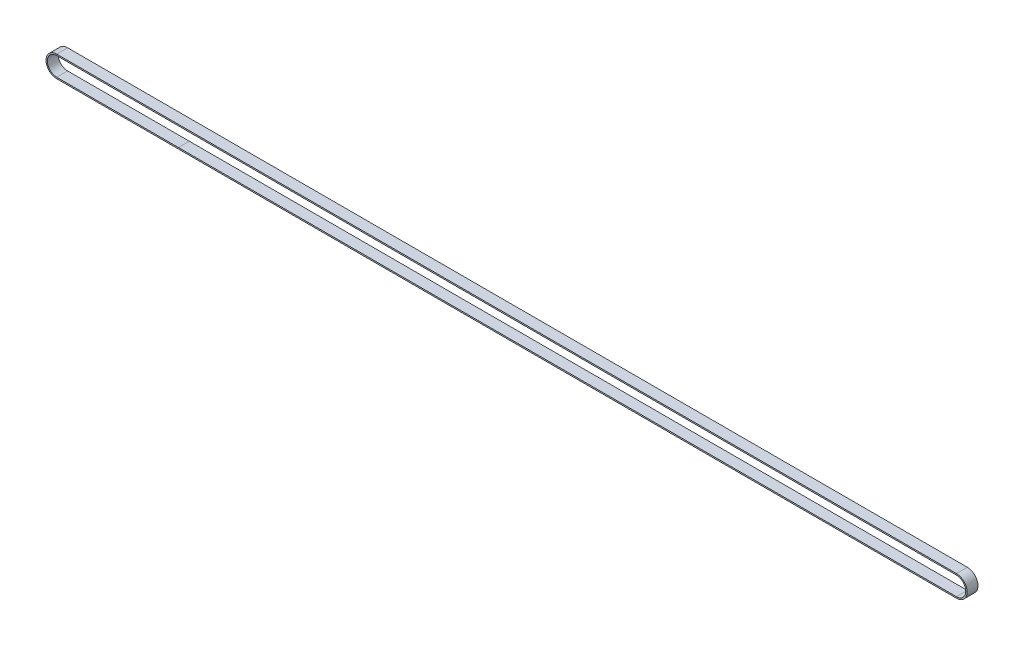
SolidWorks part; units mm, degrees
ref_plane "Front Plane" through (0, 0, 0) normal (0, 0, 1) x (1, 0, 0)
ref_plane "Top Plane" through (0, 0, 0) normal (0, 1, 0) x (1, 0, 0)
ref_plane "Right Plane" through (0, 0, 0) normal (1, 0, 0) x (0, 0, -1)
sketch "Sketch1" plane through (0, 0, 0) normal (0, 0, 1) x (1, 0, 0)
  line L0 (-149.0919, 9.0907) -> (346.9081, 9.0907)
  line L1 (-148.8622, -1.9593) -> (-148.9877, -1.9593)
  line L2 (-148.8622, -1.9593) -> (-148.8621, -1.9593)
  line L3 (-146.8622, -1.9593) -> (-146.8621, -1.9593)
  line L4 (-147.1989, -1.9593) -> (-146.8622, -1.9593)
  line L5 (-145.1989, -1.9593) -> (-144.8622, -1.9593)
  line L6 (-144.8622, -1.9593) -> (-144.8621, -1.9593)
  line L7 (-143.1989, -1.9593) -> (-142.8622, -1.9593)
  line L8 (-142.8622, -1.9593) -> (-142.8621, -1.9593)
  line L9 (-141.1989, -1.9593) -> (-140.8622, -1.9593)
  line L10 (-140.8622, -1.9593) -> (-140.8621, -1.9593)
  line L11 (-139.1989, -1.9593) -> (-138.8622, -1.9593)
  line L12 (-138.8622, -1.9593) -> (-138.8621, -1.9593)
  line L13 (-137.1989, -1.9593) -> (-136.8622, -1.9593)
  line L14 (-136.8622, -1.9593) -> (-136.8621, -1.9593)
  line L15 (-135.1989, -1.9593) -> (-134.8622, -1.9593)
  line L16 (-134.8622, -1.9593) -> (-134.8621, -1.9593)
  line L17 (-133.1989, -1.9593) -> (-132.8622, -1.9593)
  line L18 (-132.8622, -1.9593) -> (-132.8621, -1.9593)
  line L19 (-131.1989, -1.9593) -> (-130.8622, -1.9593)
  line L20 (-130.8622, -1.9593) -> (-130.8621, -1.9593)
  line L21 (-129.1989, -1.9593) -> (-128.8622, -1.9593)
  line L22 (-128.8622, -1.9593) -> (-128.8621, -1.9593)
  line L23 (-127.1989, -1.9593) -> (-126.8622, -1.9593)
  line L24 (-126.8622, -1.9593) -> (-126.8621, -1.9593)
  line L25 (-125.1989, -1.9593) -> (-124.8622, -1.9593)
  line L26 (-124.8622, -1.9593) -> (-124.8621, -1.9593)
  line L27 (-123.1989, -1.9593) -> (-122.8622, -1.9593)
  line L28 (-122.8622, -1.9593) -> (-122.8621, -1.9593)
  line L29 (-121.1989, -1.9593) -> (-120.8622, -1.9593)
  line L30 (-120.8622, -1.9593) -> (-120.8621, -1.9593)
  line L31 (-119.1989, -1.9593) -> (-118.8622, -1.9593)
  line L32 (-118.8622, -1.9593) -> (-118.8621, -1.9593)
  line L33 (-117.1989, -1.9593) -> (-116.8622, -1.9593)
  line L34 (-116.8622, -1.9593) -> (-116.8621, -1.9593)
  line L35 (-115.1989, -1.9593) -> (-114.8622, -1.9593)
  line L36 (-114.8622, -1.9593) -> (-114.8621, -1.9593)
  line L37 (-113.1989, -1.9593) -> (-112.8622, -1.9593)
  line L38 (-112.8622, -1.9593) -> (-112.8621, -1.9593)
  line L39 (-111.1989, -1.9593) -> (-110.8622, -1.9593)
  line L40 (-110.8622, -1.9593) -> (-110.8621, -1.9593)
  line L41 (-109.1989, -1.9593) -> (-108.8622, -1.9593)
  line L42 (-108.8622, -1.9593) -> (-108.8621, -1.9593)
  line L43 (-107.1989, -1.9593) -> (-106.8622, -1.9593)
  line L44 (-106.8622, -1.9593) -> (-106.8621, -1.9593)
  line L45 (-105.1989, -1.9593) -> (-104.8622, -1.9593)
  line L46 (-104.8622, -1.9593) -> (-104.8621, -1.9593)
  line L47 (-103.1989, -1.9593) -> (-102.8622, -1.9593)
  line L48 (-102.8622, -1.9593) -> (-102.8621, -1.9593)
  line L49 (-101.1989, -1.9593) -> (-100.8622, -1.9593)
  line L50 (-100.8622, -1.9593) -> (-100.8621, -1.9593)
  line L51 (-99.1989, -1.9593) -> (-98.8622, -1.9593)
  line L52 (-98.8622, -1.9593) -> (-98.8621, -1.9593)
  line L53 (-97.1989, -1.9593) -> (-96.8622, -1.9593)
  line L54 (-96.8622, -1.9593) -> (-96.8621, -1.9593)
  line L55 (-95.1989, -1.9593) -> (-94.8622, -1.9593)
  line L56 (-94.8622, -1.9593) -> (-94.8621, -1.9593)
  line L57 (-93.1989, -1.9593) -> (-92.8622, -1.9593)
  line L58 (-92.8622, -1.9593) -> (-92.8621, -1.9593)
  line L59 (-91.1989, -1.9593) -> (-90.8622, -1.9593)
  line L60 (-90.8622, -1.9593) -> (-90.8621, -1.9593)
  line L61 (-89.1989, -1.9593) -> (-88.8622, -1.9593)
  line L62 (-88.8622, -1.9593) -> (-88.8621, -1.9593)
  line L63 (-87.1989, -1.9593) -> (-86.8622, -1.9593)
  line L64 (-86.8622, -1.9593) -> (-86.8621, -1.9593)
  line L65 (-85.1989, -1.9593) -> (-84.8622, -1.9593)
  line L66 (-84.8622, -1.9593) -> (-84.8621, -1.9593)
  line L277 (346.9081, 3.1907) -> (-46.1296, 3.1907) construction
  line L278 (-83.1989, 8.3407) -> (346.9081, 8.3407)
  line L279 (-149.0919, -2.7093) -> (346.9081, -2.7093)
  line L280 (-149.1969, 8.3407) -> (-148.8622, 8.3407)
  line L491 (-84.8622, 8.3407) -> (-84.8621, 8.3407)
  line L492 (-85.1989, 8.3407) -> (-84.8622, 8.3407)
  line L493 (-86.8622, 8.3407) -> (-86.8621, 8.3407)
  line L494 (-87.1989, 8.3407) -> (-86.8622, 8.3407)
  line L495 (-88.8622, 8.3407) -> (-88.8621, 8.3407)
  line L496 (-89.1989, 8.3407) -> (-88.8622, 8.3407)
  line L497 (-90.8622, 8.3407) -> (-90.8621, 8.3407)
  line L498 (-91.1989, 8.3407) -> (-90.8622, 8.3407)
  line L499 (-92.8622, 8.3407) -> (-92.8621, 8.3407)
  line L500 (-93.1989, 8.3407) -> (-92.8622, 8.3407)
  line L501 (-94.8622, 8.3407) -> (-94.8621, 8.3407)
  line L502 (-95.1989, 8.3407) -> (-94.8622, 8.3407)
  line L503 (-96.8622, 8.3407) -> (-96.8621, 8.3407)
  line L504 (-97.1989, 8.3407) -> (-96.8622, 8.3407)
  line L505 (-98.8622, 8.3407) -> (-98.8621, 8.3407)
  line L506 (-99.1989, 8.3407) -> (-98.8622, 8.3407)
  line L507 (-100.8622, 8.3407) -> (-100.8621, 8.3407)
  line L508 (-101.1989, 8.3407) -> (-100.8622, 8.3407)
  line L509 (-102.8622, 8.3407) -> (-102.8621, 8.3407)
  line L510 (-103.1989, 8.3407) -> (-102.8622, 8.3407)
  line L511 (-104.8622, 8.3407) -> (-104.8621, 8.3407)
  line L512 (-105.1989, 8.3407) -> (-104.8622, 8.3407)
  line L513 (-106.8622, 8.3407) -> (-106.8621, 8.3407)
  line L514 (-107.1989, 8.3407) -> (-106.8622, 8.3407)
  line L515 (-108.8622, 8.3407) -> (-108.8621, 8.3407)
  line L516 (-109.1989, 8.3407) -> (-108.8622, 8.3407)
  line L517 (-110.8622, 8.3407) -> (-110.8621, 8.3407)
  line L518 (-111.1989, 8.3407) -> (-110.8622, 8.3407)
  line L519 (-112.8622, 8.3407) -> (-112.8621, 8.3407)
  line L520 (-113.1989, 8.3407) -> (-112.8622, 8.3407)
  line L521 (-114.8622, 8.3407) -> (-114.8621, 8.3407)
  line L522 (-115.1989, 8.3407) -> (-114.8622, 8.3407)
  line L523 (-116.8622, 8.3407) -> (-116.8621, 8.3407)
  line L524 (-117.1989, 8.3407) -> (-116.8622, 8.3407)
  line L525 (-118.8622, 8.3407) -> (-118.8621, 8.3407)
  line L526 (-119.1989, 8.3407) -> (-118.8622, 8.3407)
  line L527 (-120.8622, 8.3407) -> (-120.8621, 8.3407)
  line L528 (-121.1989, 8.3407) -> (-120.8622, 8.3407)
  line L529 (-122.8622, 8.3407) -> (-122.8621, 8.3407)
  line L530 (-123.1989, 8.3407) -> (-122.8622, 8.3407)
  line L531 (-124.8622, 8.3407) -> (-124.8621, 8.3407)
  line L532 (-125.1989, 8.3407) -> (-124.8622, 8.3407)
  line L533 (-126.8622, 8.3407) -> (-126.8621, 8.3407)
  line L534 (-127.1989, 8.3407) -> (-126.8622, 8.3407)
  line L535 (-128.8622, 8.3407) -> (-128.8621, 8.3407)
  line L536 (-129.1989, 8.3407) -> (-128.8622, 8.3407)
  line L537 (-130.8622, 8.3407) -> (-130.8621, 8.3407)
  line L538 (-131.1989, 8.3407) -> (-130.8622, 8.3407)
  line L539 (-132.8622, 8.3407) -> (-132.8621, 8.3407)
  line L540 (-133.1989, 8.3407) -> (-132.8622, 8.3407)
  line L541 (-134.8622, 8.3407) -> (-134.8621, 8.3407)
  line L542 (-135.1989, 8.3407) -> (-134.8622, 8.3407)
  line L543 (-136.8622, 8.3407) -> (-136.8621, 8.3407)
  line L544 (-137.1989, 8.3407) -> (-136.8622, 8.3407)
  line L545 (-138.8622, 8.3407) -> (-138.8621, 8.3407)
  line L546 (-139.1989, 8.3407) -> (-138.8622, 8.3407)
  line L547 (-140.8622, 8.3407) -> (-140.8621, 8.3407)
  line L548 (-141.1989, 8.3407) -> (-140.8622, 8.3407)
  line L549 (-142.8622, 8.3407) -> (-142.8621, 8.3407)
  line L550 (-143.1989, 8.3407) -> (-142.8622, 8.3407)
  line L551 (-144.8622, 8.3407) -> (-144.8621, 8.3407)
  line L552 (-145.1989, 8.3407) -> (-144.8622, 8.3407)
  line L553 (-147.1989, 8.3407) -> (-146.8622, 8.3407)
  line L554 (-146.8622, 8.3407) -> (-146.8621, 8.3407)
  line L555 (-148.8622, 8.3407) -> (-148.8621, 8.3407)
  line L556 (-83.1989, -1.9593) -> (346.9081, -1.9593)
  arc A0 (-149.1969, 8.3407) -> (-148.9869, -1.9593) centre (-149.0919, 3.1907) ccw
  arc A1 (346.9081, -1.9593) -> (346.9081, 8.3407) centre (346.9081, 3.1907) ccw
  arc A2 (-146.8621, -1.9593) -> (-146.7228, -1.8564) centre (-146.9197, -1.7354) ccw
  arc A3 (-148.8621, -1.9593) -> (-148.7228, -1.8564) centre (-148.9197, -1.7354) ccw
  arc A4 (-148.7228, -1.8564) -> (-148.6336, -1.611) centre (-149.2769, -1.5162) ccw
  arc A5 (-147.4274, -1.611) -> (-148.6336, -1.611) centre (-148.0305, -1.6999) ccw
  arc A6 (-147.4274, -1.611) -> (-147.3383, -1.8564) centre (-146.7842, -1.5162) ccw
  arc A7 (-147.3383, -1.8564) -> (-147.1989, -1.9593) centre (-147.1413, -1.7354) ccw
  arc A8 (-146.7228, -1.8564) -> (-146.6336, -1.611) centre (-147.2769, -1.5162) ccw
  arc A9 (-145.4274, -1.611) -> (-146.6336, -1.611) centre (-146.0305, -1.6999) ccw
  arc A10 (-145.4274, -1.611) -> (-145.3383, -1.8564) centre (-144.7842, -1.5162) ccw
  arc A11 (-145.3383, -1.8564) -> (-145.1989, -1.9593) centre (-145.1413, -1.7354) ccw
  arc A12 (-144.8621, -1.9593) -> (-144.7228, -1.8564) centre (-144.9197, -1.7354) ccw
  arc A13 (-144.7228, -1.8564) -> (-144.6336, -1.611) centre (-145.2769, -1.5162) ccw
  arc A14 (-143.4274, -1.611) -> (-144.6336, -1.611) centre (-144.0305, -1.6999) ccw
  arc A15 (-143.4274, -1.611) -> (-143.3383, -1.8564) centre (-142.7842, -1.5162) ccw
  arc A16 (-143.3383, -1.8564) -> (-143.1989, -1.9593) centre (-143.1413, -1.7354) ccw
  arc A17 (-142.8621, -1.9593) -> (-142.7228, -1.8564) centre (-142.9197, -1.7354) ccw
  arc A18 (-142.7228, -1.8564) -> (-142.6336, -1.611) centre (-143.2769, -1.5162) ccw
  arc A19 (-141.4274, -1.611) -> (-142.6336, -1.611) centre (-142.0305, -1.6999) ccw
  arc A20 (-141.4274, -1.611) -> (-141.3383, -1.8564) centre (-140.7842, -1.5162) ccw
  arc A21 (-141.3383, -1.8564) -> (-141.1989, -1.9593) centre (-141.1413, -1.7354) ccw
  arc A22 (-140.8621, -1.9593) -> (-140.7228, -1.8564) centre (-140.9197, -1.7354) ccw
  arc A23 (-140.7228, -1.8564) -> (-140.6336, -1.611) centre (-141.2769, -1.5162) ccw
  arc A24 (-139.4274, -1.611) -> (-140.6336, -1.611) centre (-140.0305, -1.6999) ccw
  arc A25 (-139.4274, -1.611) -> (-139.3383, -1.8564) centre (-138.7842, -1.5162) ccw
  arc A26 (-139.3383, -1.8564) -> (-139.1989, -1.9593) centre (-139.1413, -1.7354) ccw
  arc A27 (-138.8621, -1.9593) -> (-138.7228, -1.8564) centre (-138.9197, -1.7354) ccw
  arc A28 (-138.7228, -1.8564) -> (-138.6336, -1.611) centre (-139.2769, -1.5162) ccw
  arc A29 (-137.4274, -1.611) -> (-138.6336, -1.611) centre (-138.0305, -1.6999) ccw
  arc A30 (-137.4274, -1.611) -> (-137.3383, -1.8564) centre (-136.7842, -1.5162) ccw
  arc A31 (-137.3383, -1.8564) -> (-137.1989, -1.9593) centre (-137.1413, -1.7354) ccw
  arc A32 (-136.8621, -1.9593) -> (-136.7228, -1.8564) centre (-136.9197, -1.7354) ccw
  arc A33 (-136.7228, -1.8564) -> (-136.6336, -1.611) centre (-137.2769, -1.5162) ccw
  arc A34 (-135.4274, -1.611) -> (-136.6336, -1.611) centre (-136.0305, -1.6999) ccw
  arc A35 (-135.4274, -1.611) -> (-135.3383, -1.8564) centre (-134.7842, -1.5162) ccw
  arc A36 (-135.3383, -1.8564) -> (-135.1989, -1.9593) centre (-135.1413, -1.7354) ccw
  arc A37 (-134.8621, -1.9593) -> (-134.7228, -1.8564) centre (-134.9197, -1.7354) ccw
  arc A38 (-134.7228, -1.8564) -> (-134.6336, -1.611) centre (-135.2769, -1.5162) ccw
  arc A39 (-133.4274, -1.611) -> (-134.6336, -1.611) centre (-134.0305, -1.6999) ccw
  arc A40 (-133.4274, -1.611) -> (-133.3383, -1.8564) centre (-132.7842, -1.5162) ccw
  arc A41 (-133.3383, -1.8564) -> (-133.1989, -1.9593) centre (-133.1413, -1.7354) ccw
  arc A42 (-132.8621, -1.9593) -> (-132.7228, -1.8564) centre (-132.9197, -1.7354) ccw
  arc A43 (-132.7228, -1.8564) -> (-132.6336, -1.611) centre (-133.2769, -1.5162) ccw
  arc A44 (-131.4274, -1.611) -> (-132.6336, -1.611) centre (-132.0305, -1.6999) ccw
  arc A45 (-131.4274, -1.611) -> (-131.3383, -1.8564) centre (-130.7842, -1.5162) ccw
  arc A46 (-131.3383, -1.8564) -> (-131.1989, -1.9593) centre (-131.1413, -1.7354) ccw
  arc A47 (-130.8621, -1.9593) -> (-130.7228, -1.8564) centre (-130.9197, -1.7354) ccw
  arc A48 (-130.7228, -1.8564) -> (-130.6336, -1.611) centre (-131.2769, -1.5162) ccw
  arc A49 (-129.4274, -1.611) -> (-130.6336, -1.611) centre (-130.0305, -1.6999) ccw
  arc A50 (-129.4274, -1.611) -> (-129.3383, -1.8564) centre (-128.7842, -1.5162) ccw
  arc A51 (-129.3383, -1.8564) -> (-129.1989, -1.9593) centre (-129.1413, -1.7354) ccw
  arc A52 (-128.8621, -1.9593) -> (-128.7228, -1.8564) centre (-128.9197, -1.7354) ccw
  arc A53 (-128.7228, -1.8564) -> (-128.6336, -1.611) centre (-129.2769, -1.5162) ccw
  arc A54 (-127.4274, -1.611) -> (-128.6336, -1.611) centre (-128.0305, -1.6999) ccw
  arc A55 (-127.4274, -1.611) -> (-127.3383, -1.8564) centre (-126.7842, -1.5162) ccw
  arc A56 (-127.3383, -1.8564) -> (-127.1989, -1.9593) centre (-127.1413, -1.7354) ccw
  arc A57 (-126.8621, -1.9593) -> (-126.7228, -1.8564) centre (-126.9197, -1.7354) ccw
  arc A58 (-126.7228, -1.8564) -> (-126.6336, -1.611) centre (-127.2769, -1.5162) ccw
  arc A59 (-125.4274, -1.611) -> (-126.6336, -1.611) centre (-126.0305, -1.6999) ccw
  arc A60 (-125.4274, -1.611) -> (-125.3383, -1.8564) centre (-124.7842, -1.5162) ccw
  arc A61 (-125.3383, -1.8564) -> (-125.1989, -1.9593) centre (-125.1413, -1.7354) ccw
  arc A62 (-124.8621, -1.9593) -> (-124.7228, -1.8564) centre (-124.9197, -1.7354) ccw
  arc A63 (-124.7228, -1.8564) -> (-124.6336, -1.611) centre (-125.2769, -1.5162) ccw
  arc A64 (-123.4274, -1.611) -> (-124.6336, -1.611) centre (-124.0305, -1.6999) ccw
  arc A65 (-123.4274, -1.611) -> (-123.3383, -1.8564) centre (-122.7842, -1.5162) ccw
  arc A66 (-123.3383, -1.8564) -> (-123.1989, -1.9593) centre (-123.1413, -1.7354) ccw
  arc A67 (-122.8621, -1.9593) -> (-122.7228, -1.8564) centre (-122.9197, -1.7354) ccw
  arc A68 (-122.7228, -1.8564) -> (-122.6336, -1.611) centre (-123.2769, -1.5162) ccw
  arc A69 (-121.4274, -1.611) -> (-122.6336, -1.611) centre (-122.0305, -1.6999) ccw
  arc A70 (-121.4274, -1.611) -> (-121.3383, -1.8564) centre (-120.7842, -1.5162) ccw
  arc A71 (-121.3383, -1.8564) -> (-121.1989, -1.9593) centre (-121.1413, -1.7354) ccw
  arc A72 (-120.8621, -1.9593) -> (-120.7228, -1.8564) centre (-120.9197, -1.7354) ccw
  arc A73 (-120.7228, -1.8564) -> (-120.6336, -1.611) centre (-121.2769, -1.5162) ccw
  arc A74 (-119.4274, -1.611) -> (-120.6336, -1.611) centre (-120.0305, -1.6999) ccw
  arc A75 (-119.4274, -1.611) -> (-119.3383, -1.8564) centre (-118.7842, -1.5162) ccw
  arc A76 (-119.3383, -1.8564) -> (-119.1989, -1.9593) centre (-119.1413, -1.7354) ccw
  arc A77 (-118.8621, -1.9593) -> (-118.7228, -1.8564) centre (-118.9197, -1.7354) ccw
  arc A78 (-118.7228, -1.8564) -> (-118.6336, -1.611) centre (-119.2769, -1.5162) ccw
  arc A79 (-117.4274, -1.611) -> (-118.6336, -1.611) centre (-118.0305, -1.6999) ccw
  arc A80 (-117.4274, -1.611) -> (-117.3383, -1.8564) centre (-116.7842, -1.5162) ccw
  arc A81 (-117.3383, -1.8564) -> (-117.1989, -1.9593) centre (-117.1413, -1.7354) ccw
  arc A82 (-116.8621, -1.9593) -> (-116.7228, -1.8564) centre (-116.9197, -1.7354) ccw
  arc A83 (-116.7228, -1.8564) -> (-116.6336, -1.611) centre (-117.2769, -1.5162) ccw
  arc A84 (-115.4274, -1.611) -> (-116.6336, -1.611) centre (-116.0305, -1.6999) ccw
  arc A85 (-115.4274, -1.611) -> (-115.3383, -1.8564) centre (-114.7842, -1.5162) ccw
  arc A86 (-115.3383, -1.8564) -> (-115.1989, -1.9593) centre (-115.1413, -1.7354) ccw
  arc A87 (-114.8621, -1.9593) -> (-114.7228, -1.8564) centre (-114.9197, -1.7354) ccw
  arc A88 (-114.7228, -1.8564) -> (-114.6336, -1.611) centre (-115.2769, -1.5162) ccw
  arc A89 (-113.4274, -1.611) -> (-114.6336, -1.611) centre (-114.0305, -1.6999) ccw
  arc A90 (-113.4274, -1.611) -> (-113.3383, -1.8564) centre (-112.7842, -1.5162) ccw
  arc A91 (-113.3383, -1.8564) -> (-113.1989, -1.9593) centre (-113.1413, -1.7354) ccw
  arc A92 (-112.8621, -1.9593) -> (-112.7228, -1.8564) centre (-112.9197, -1.7354) ccw
  arc A93 (-112.7228, -1.8564) -> (-112.6336, -1.611) centre (-113.2769, -1.5162) ccw
  arc A94 (-111.4274, -1.611) -> (-112.6336, -1.611) centre (-112.0305, -1.6999) ccw
  arc A95 (-111.4274, -1.611) -> (-111.3383, -1.8564) centre (-110.7842, -1.5162) ccw
  arc A96 (-111.3383, -1.8564) -> (-111.1989, -1.9593) centre (-111.1413, -1.7354) ccw
  arc A97 (-110.8621, -1.9593) -> (-110.7228, -1.8564) centre (-110.9197, -1.7354) ccw
  arc A98 (-110.7228, -1.8564) -> (-110.6336, -1.611) centre (-111.2769, -1.5162) ccw
  arc A99 (-109.4274, -1.611) -> (-110.6336, -1.611) centre (-110.0305, -1.6999) ccw
  arc A100 (-109.4274, -1.611) -> (-109.3383, -1.8564) centre (-108.7842, -1.5162) ccw
  arc A101 (-109.3383, -1.8564) -> (-109.1989, -1.9593) centre (-109.1413, -1.7354) ccw
  arc A102 (-108.8621, -1.9593) -> (-108.7228, -1.8564) centre (-108.9197, -1.7354) ccw
  arc A103 (-108.7228, -1.8564) -> (-108.6336, -1.611) centre (-109.2769, -1.5162) ccw
  arc A104 (-107.4274, -1.611) -> (-108.6336, -1.611) centre (-108.0305, -1.6999) ccw
  arc A105 (-107.4274, -1.611) -> (-107.3383, -1.8564) centre (-106.7842, -1.5162) ccw
  arc A106 (-107.3383, -1.8564) -> (-107.1989, -1.9593) centre (-107.1413, -1.7354) ccw
  arc A107 (-106.8621, -1.9593) -> (-106.7228, -1.8564) centre (-106.9197, -1.7354) ccw
  arc A108 (-106.7228, -1.8564) -> (-106.6336, -1.611) centre (-107.2769, -1.5162) ccw
  arc A109 (-105.4274, -1.611) -> (-106.6336, -1.611) centre (-106.0305, -1.6999) ccw
  arc A110 (-105.4274, -1.611) -> (-105.3383, -1.8564) centre (-104.7842, -1.5162) ccw
  arc A111 (-105.3383, -1.8564) -> (-105.1989, -1.9593) centre (-105.1413, -1.7354) ccw
  arc A112 (-104.8621, -1.9593) -> (-104.7228, -1.8564) centre (-104.9197, -1.7354) ccw
  arc A113 (-104.7228, -1.8564) -> (-104.6336, -1.611) centre (-105.2769, -1.5162) ccw
  arc A114 (-103.4274, -1.611) -> (-104.6336, -1.611) centre (-104.0305, -1.6999) ccw
  arc A115 (-103.4274, -1.611) -> (-103.3383, -1.8564) centre (-102.7842, -1.5162) ccw
  arc A116 (-103.3383, -1.8564) -> (-103.1989, -1.9593) centre (-103.1413, -1.7354) ccw
  arc A117 (-102.8621, -1.9593) -> (-102.7228, -1.8564) centre (-102.9197, -1.7354) ccw
  arc A118 (-102.7228, -1.8564) -> (-102.6336, -1.611) centre (-103.2769, -1.5162) ccw
  arc A119 (-101.4274, -1.611) -> (-102.6336, -1.611) centre (-102.0305, -1.6999) ccw
  arc A120 (-101.4274, -1.611) -> (-101.3383, -1.8564) centre (-100.7842, -1.5162) ccw
  arc A121 (-101.3383, -1.8564) -> (-101.1989, -1.9593) centre (-101.1413, -1.7354) ccw
  arc A122 (-100.8621, -1.9593) -> (-100.7228, -1.8564) centre (-100.9197, -1.7354) ccw
  arc A123 (-100.7228, -1.8564) -> (-100.6336, -1.611) centre (-101.2769, -1.5162) ccw
  arc A124 (-99.4274, -1.611) -> (-100.6336, -1.611) centre (-100.0305, -1.6999) ccw
  arc A125 (-99.4274, -1.611) -> (-99.3383, -1.8564) centre (-98.7842, -1.5162) ccw
  arc A126 (-99.3383, -1.8564) -> (-99.1989, -1.9593) centre (-99.1413, -1.7354) ccw
  arc A127 (-98.8621, -1.9593) -> (-98.7228, -1.8564) centre (-98.9197, -1.7354) ccw
  arc A128 (-98.7228, -1.8564) -> (-98.6336, -1.611) centre (-99.2769, -1.5162) ccw
  arc A129 (-97.4274, -1.611) -> (-98.6336, -1.611) centre (-98.0305, -1.6999) ccw
  arc A130 (-97.4274, -1.611) -> (-97.3383, -1.8564) centre (-96.7842, -1.5162) ccw
  arc A131 (-97.3383, -1.8564) -> (-97.1989, -1.9593) centre (-97.1413, -1.7354) ccw
  arc A132 (-96.8621, -1.9593) -> (-96.7228, -1.8564) centre (-96.9197, -1.7354) ccw
  arc A133 (-96.7228, -1.8564) -> (-96.6336, -1.611) centre (-97.2769, -1.5162) ccw
  arc A134 (-95.4274, -1.611) -> (-96.6336, -1.611) centre (-96.0305, -1.6999) ccw
  arc A135 (-95.4274, -1.611) -> (-95.3383, -1.8564) centre (-94.7842, -1.5162) ccw
  arc A136 (-95.3383, -1.8564) -> (-95.1989, -1.9593) centre (-95.1413, -1.7354) ccw
  arc A137 (-94.8621, -1.9593) -> (-94.7228, -1.8564) centre (-94.9197, -1.7354) ccw
  arc A138 (-94.7228, -1.8564) -> (-94.6336, -1.611) centre (-95.2769, -1.5162) ccw
  arc A139 (-93.4274, -1.611) -> (-94.6336, -1.611) centre (-94.0305, -1.6999) ccw
  arc A140 (-93.4274, -1.611) -> (-93.3383, -1.8564) centre (-92.7842, -1.5162) ccw
  arc A141 (-93.3383, -1.8564) -> (-93.1989, -1.9593) centre (-93.1413, -1.7354) ccw
  arc A142 (-92.8621, -1.9593) -> (-92.7228, -1.8564) centre (-92.9197, -1.7354) ccw
  arc A143 (-92.7228, -1.8564) -> (-92.6336, -1.611) centre (-93.2769, -1.5162) ccw
  arc A144 (-91.4274, -1.611) -> (-92.6336, -1.611) centre (-92.0305, -1.6999) ccw
  arc A145 (-91.4274, -1.611) -> (-91.3383, -1.8564) centre (-90.7842, -1.5162) ccw
  arc A146 (-91.3383, -1.8564) -> (-91.1989, -1.9593) centre (-91.1413, -1.7354) ccw
  arc A147 (-90.8621, -1.9593) -> (-90.7228, -1.8564) centre (-90.9197, -1.7354) ccw
  arc A148 (-90.7228, -1.8564) -> (-90.6336, -1.611) centre (-91.2769, -1.5162) ccw
  arc A149 (-89.4274, -1.611) -> (-90.6336, -1.611) centre (-90.0305, -1.6999) ccw
  arc A150 (-89.4274, -1.611) -> (-89.3383, -1.8564) centre (-88.7842, -1.5162) ccw
  arc A151 (-89.3383, -1.8564) -> (-89.1989, -1.9593) centre (-89.1413, -1.7354) ccw
  arc A152 (-88.8621, -1.9593) -> (-88.7228, -1.8564) centre (-88.9197, -1.7354) ccw
  arc A153 (-88.7228, -1.8564) -> (-88.6336, -1.611) centre (-89.2769, -1.5162) ccw
  arc A154 (-87.4274, -1.611) -> (-88.6336, -1.611) centre (-88.0305, -1.6999) ccw
  arc A155 (-87.4274, -1.611) -> (-87.3383, -1.8564) centre (-86.7842, -1.5162) ccw
  arc A156 (-87.3383, -1.8564) -> (-87.1989, -1.9593) centre (-87.1413, -1.7354) ccw
  arc A157 (-86.8621, -1.9593) -> (-86.7228, -1.8564) centre (-86.9197, -1.7354) ccw
  arc A158 (-86.7228, -1.8564) -> (-86.6336, -1.611) centre (-87.2769, -1.5162) ccw
  arc A159 (-85.4274, -1.611) -> (-86.6336, -1.611) centre (-86.0305, -1.6999) ccw
  arc A160 (-85.4274, -1.611) -> (-85.3383, -1.8564) centre (-84.7842, -1.5162) ccw
  arc A161 (-85.3383, -1.8564) -> (-85.1989, -1.9593) centre (-85.1413, -1.7354) ccw
  arc A162 (-84.8621, -1.9593) -> (-84.7228, -1.8564) centre (-84.9197, -1.7354) ccw
  arc A163 (-84.7228, -1.8564) -> (-84.6336, -1.611) centre (-85.2769, -1.5162) ccw
  arc A164 (-83.4274, -1.611) -> (-84.6336, -1.611) centre (-84.0305, -1.6999) ccw
  arc A165 (-83.4274, -1.611) -> (-83.3383, -1.8564) centre (-82.7842, -1.5162) ccw
  arc A166 (-83.3383, -1.8564) -> (-83.1989, -1.9593) centre (-83.1413, -1.7354) ccw
  arc A692 (-149.0919, 9.0907) -> (-149.0919, -2.7093) centre (-149.0919, 3.1907) ccw
  arc A693 (346.9081, -2.7093) -> (346.9081, 9.0907) centre (346.9081, 3.1907) ccw
  arc A1219 (-83.3383, 8.2378) -> (-83.1989, 8.3407) centre (-83.1413, 8.1169) cw
  arc A1220 (-83.4274, 7.9924) -> (-83.3383, 8.2378) centre (-82.7842, 7.8976) cw
  arc A1221 (-83.4274, 7.9924) -> (-84.6336, 7.9924) centre (-84.0305, 8.0813) cw
  arc A1222 (-84.7228, 8.2378) -> (-84.6336, 7.9924) centre (-85.2769, 7.8976) cw
  arc A1223 (-84.8621, 8.3407) -> (-84.7228, 8.2378) centre (-84.9197, 8.1169) cw
  arc A1224 (-85.3383, 8.2378) -> (-85.1989, 8.3407) centre (-85.1413, 8.1169) cw
  arc A1225 (-85.4274, 7.9924) -> (-85.3383, 8.2378) centre (-84.7842, 7.8976) cw
  arc A1226 (-85.4274, 7.9924) -> (-86.6336, 7.9924) centre (-86.0305, 8.0813) cw
  arc A1227 (-86.7228, 8.2378) -> (-86.6336, 7.9924) centre (-87.2769, 7.8976) cw
  arc A1228 (-86.8621, 8.3407) -> (-86.7228, 8.2378) centre (-86.9197, 8.1169) cw
  arc A1229 (-87.3383, 8.2378) -> (-87.1989, 8.3407) centre (-87.1413, 8.1169) cw
  arc A1230 (-87.4274, 7.9924) -> (-87.3383, 8.2378) centre (-86.7842, 7.8976) cw
  arc A1231 (-87.4274, 7.9924) -> (-88.6336, 7.9924) centre (-88.0305, 8.0813) cw
  arc A1232 (-88.7228, 8.2378) -> (-88.6336, 7.9924) centre (-89.2769, 7.8976) cw
  arc A1233 (-88.8621, 8.3407) -> (-88.7228, 8.2378) centre (-88.9197, 8.1169) cw
  arc A1234 (-89.3383, 8.2378) -> (-89.1989, 8.3407) centre (-89.1413, 8.1169) cw
  arc A1235 (-89.4274, 7.9924) -> (-89.3383, 8.2378) centre (-88.7842, 7.8976) cw
  arc A1236 (-89.4274, 7.9924) -> (-90.6336, 7.9924) centre (-90.0305, 8.0813) cw
  arc A1237 (-90.7228, 8.2378) -> (-90.6336, 7.9924) centre (-91.2769, 7.8976) cw
  arc A1238 (-90.8621, 8.3407) -> (-90.7228, 8.2378) centre (-90.9197, 8.1169) cw
  arc A1239 (-91.3383, 8.2378) -> (-91.1989, 8.3407) centre (-91.1413, 8.1169) cw
  arc A1240 (-91.4274, 7.9924) -> (-91.3383, 8.2378) centre (-90.7842, 7.8976) cw
  arc A1241 (-91.4274, 7.9924) -> (-92.6336, 7.9924) centre (-92.0305, 8.0813) cw
  arc A1242 (-92.7228, 8.2378) -> (-92.6336, 7.9924) centre (-93.2769, 7.8976) cw
  arc A1243 (-92.8621, 8.3407) -> (-92.7228, 8.2378) centre (-92.9197, 8.1169) cw
  arc A1244 (-93.3383, 8.2378) -> (-93.1989, 8.3407) centre (-93.1413, 8.1169) cw
  arc A1245 (-93.4274, 7.9924) -> (-93.3383, 8.2378) centre (-92.7842, 7.8976) cw
  arc A1246 (-93.4274, 7.9924) -> (-94.6336, 7.9924) centre (-94.0305, 8.0813) cw
  arc A1247 (-94.7228, 8.2378) -> (-94.6336, 7.9924) centre (-95.2769, 7.8976) cw
  arc A1248 (-94.8621, 8.3407) -> (-94.7228, 8.2378) centre (-94.9197, 8.1169) cw
  arc A1249 (-95.3383, 8.2378) -> (-95.1989, 8.3407) centre (-95.1413, 8.1169) cw
  arc A1250 (-95.4274, 7.9924) -> (-95.3383, 8.2378) centre (-94.7842, 7.8976) cw
  arc A1251 (-95.4274, 7.9924) -> (-96.6336, 7.9924) centre (-96.0305, 8.0813) cw
  arc A1252 (-96.7228, 8.2378) -> (-96.6336, 7.9924) centre (-97.2769, 7.8976) cw
  arc A1253 (-96.8621, 8.3407) -> (-96.7228, 8.2378) centre (-96.9197, 8.1169) cw
  arc A1254 (-97.3383, 8.2378) -> (-97.1989, 8.3407) centre (-97.1413, 8.1169) cw
  arc A1255 (-97.4274, 7.9924) -> (-97.3383, 8.2378) centre (-96.7842, 7.8976) cw
  arc A1256 (-97.4274, 7.9924) -> (-98.6336, 7.9924) centre (-98.0305, 8.0813) cw
  arc A1257 (-98.7228, 8.2378) -> (-98.6336, 7.9924) centre (-99.2769, 7.8976) cw
  arc A1258 (-98.8621, 8.3407) -> (-98.7228, 8.2378) centre (-98.9197, 8.1169) cw
  arc A1259 (-99.3383, 8.2378) -> (-99.1989, 8.3407) centre (-99.1413, 8.1169) cw
  arc A1260 (-99.4274, 7.9924) -> (-99.3383, 8.2378) centre (-98.7842, 7.8976) cw
  arc A1261 (-99.4274, 7.9924) -> (-100.6336, 7.9924) centre (-100.0305, 8.0813) cw
  arc A1262 (-100.7228, 8.2378) -> (-100.6336, 7.9924) centre (-101.2769, 7.8976) cw
  arc A1263 (-100.8621, 8.3407) -> (-100.7228, 8.2378) centre (-100.9197, 8.1169) cw
  arc A1264 (-101.3383, 8.2378) -> (-101.1989, 8.3407) centre (-101.1413, 8.1169) cw
  arc A1265 (-101.4274, 7.9924) -> (-101.3383, 8.2378) centre (-100.7842, 7.8976) cw
  arc A1266 (-101.4274, 7.9924) -> (-102.6336, 7.9924) centre (-102.0305, 8.0813) cw
  arc A1267 (-102.7228, 8.2378) -> (-102.6336, 7.9924) centre (-103.2769, 7.8976) cw
  arc A1268 (-102.8621, 8.3407) -> (-102.7228, 8.2378) centre (-102.9197, 8.1169) cw
  arc A1269 (-103.3383, 8.2378) -> (-103.1989, 8.3407) centre (-103.1413, 8.1169) cw
  arc A1270 (-103.4274, 7.9924) -> (-103.3383, 8.2378) centre (-102.7842, 7.8976) cw
  arc A1271 (-103.4274, 7.9924) -> (-104.6336, 7.9924) centre (-104.0305, 8.0813) cw
  arc A1272 (-104.7228, 8.2378) -> (-104.6336, 7.9924) centre (-105.2769, 7.8976) cw
  arc A1273 (-104.8621, 8.3407) -> (-104.7228, 8.2378) centre (-104.9197, 8.1169) cw
  arc A1274 (-105.3383, 8.2378) -> (-105.1989, 8.3407) centre (-105.1413, 8.1169) cw
  arc A1275 (-105.4274, 7.9924) -> (-105.3383, 8.2378) centre (-104.7842, 7.8976) cw
  arc A1276 (-105.4274, 7.9924) -> (-106.6336, 7.9924) centre (-106.0305, 8.0813) cw
  arc A1277 (-106.7228, 8.2378) -> (-106.6336, 7.9924) centre (-107.2769, 7.8976) cw
  arc A1278 (-106.8621, 8.3407) -> (-106.7228, 8.2378) centre (-106.9197, 8.1169) cw
  arc A1279 (-107.3383, 8.2378) -> (-107.1989, 8.3407) centre (-107.1413, 8.1169) cw
  arc A1280 (-107.4274, 7.9924) -> (-107.3383, 8.2378) centre (-106.7842, 7.8976) cw
  arc A1281 (-107.4274, 7.9924) -> (-108.6336, 7.9924) centre (-108.0305, 8.0813) cw
  arc A1282 (-108.7228, 8.2378) -> (-108.6336, 7.9924) centre (-109.2769, 7.8976) cw
  arc A1283 (-108.8621, 8.3407) -> (-108.7228, 8.2378) centre (-108.9197, 8.1169) cw
  arc A1284 (-109.3383, 8.2378) -> (-109.1989, 8.3407) centre (-109.1413, 8.1169) cw
  arc A1285 (-109.4274, 7.9924) -> (-109.3383, 8.2378) centre (-108.7842, 7.8976) cw
  arc A1286 (-109.4274, 7.9924) -> (-110.6336, 7.9924) centre (-110.0305, 8.0813) cw
  arc A1287 (-110.7228, 8.2378) -> (-110.6336, 7.9924) centre (-111.2769, 7.8976) cw
  arc A1288 (-110.8621, 8.3407) -> (-110.7228, 8.2378) centre (-110.9197, 8.1169) cw
  arc A1289 (-111.3383, 8.2378) -> (-111.1989, 8.3407) centre (-111.1413, 8.1169) cw
  arc A1290 (-111.4274, 7.9924) -> (-111.3383, 8.2378) centre (-110.7842, 7.8976) cw
  arc A1291 (-111.4274, 7.9924) -> (-112.6336, 7.9924) centre (-112.0305, 8.0813) cw
  arc A1292 (-112.7228, 8.2378) -> (-112.6336, 7.9924) centre (-113.2769, 7.8976) cw
  arc A1293 (-112.8621, 8.3407) -> (-112.7228, 8.2378) centre (-112.9197, 8.1169) cw
  arc A1294 (-113.3383, 8.2378) -> (-113.1989, 8.3407) centre (-113.1413, 8.1169) cw
  arc A1295 (-113.4274, 7.9924) -> (-113.3383, 8.2378) centre (-112.7842, 7.8976) cw
  arc A1296 (-113.4274, 7.9924) -> (-114.6336, 7.9924) centre (-114.0305, 8.0813) cw
  arc A1297 (-114.7228, 8.2378) -> (-114.6336, 7.9924) centre (-115.2769, 7.8976) cw
  arc A1298 (-114.8621, 8.3407) -> (-114.7228, 8.2378) centre (-114.9197, 8.1169) cw
  arc A1299 (-115.3383, 8.2378) -> (-115.1989, 8.3407) centre (-115.1413, 8.1169) cw
  arc A1300 (-115.4274, 7.9924) -> (-115.3383, 8.2378) centre (-114.7842, 7.8976) cw
  arc A1301 (-115.4274, 7.9924) -> (-116.6336, 7.9924) centre (-116.0305, 8.0813) cw
  arc A1302 (-116.7228, 8.2378) -> (-116.6336, 7.9924) centre (-117.2769, 7.8976) cw
  arc A1303 (-116.8621, 8.3407) -> (-116.7228, 8.2378) centre (-116.9197, 8.1169) cw
  arc A1304 (-117.3383, 8.2378) -> (-117.1989, 8.3407) centre (-117.1413, 8.1169) cw
  arc A1305 (-117.4274, 7.9924) -> (-117.3383, 8.2378) centre (-116.7842, 7.8976) cw
  arc A1306 (-117.4274, 7.9924) -> (-118.6336, 7.9924) centre (-118.0305, 8.0813) cw
  arc A1307 (-118.7228, 8.2378) -> (-118.6336, 7.9924) centre (-119.2769, 7.8976) cw
  arc A1308 (-118.8621, 8.3407) -> (-118.7228, 8.2378) centre (-118.9197, 8.1169) cw
  arc A1309 (-119.3383, 8.2378) -> (-119.1989, 8.3407) centre (-119.1413, 8.1169) cw
  arc A1310 (-119.4274, 7.9924) -> (-119.3383, 8.2378) centre (-118.7842, 7.8976) cw
  arc A1311 (-119.4274, 7.9924) -> (-120.6336, 7.9924) centre (-120.0305, 8.0813) cw
  arc A1312 (-120.7228, 8.2378) -> (-120.6336, 7.9924) centre (-121.2769, 7.8976) cw
  arc A1313 (-120.8621, 8.3407) -> (-120.7228, 8.2378) centre (-120.9197, 8.1169) cw
  arc A1314 (-121.3383, 8.2378) -> (-121.1989, 8.3407) centre (-121.1413, 8.1169) cw
  arc A1315 (-121.4274, 7.9924) -> (-121.3383, 8.2378) centre (-120.7842, 7.8976) cw
  arc A1316 (-121.4274, 7.9924) -> (-122.6336, 7.9924) centre (-122.0305, 8.0813) cw
  arc A1317 (-122.7228, 8.2378) -> (-122.6336, 7.9924) centre (-123.2769, 7.8976) cw
  arc A1318 (-122.8621, 8.3407) -> (-122.7228, 8.2378) centre (-122.9197, 8.1169) cw
  arc A1319 (-123.3383, 8.2378) -> (-123.1989, 8.3407) centre (-123.1413, 8.1169) cw
  arc A1320 (-123.4274, 7.9924) -> (-123.3383, 8.2378) centre (-122.7842, 7.8976) cw
  arc A1321 (-123.4274, 7.9924) -> (-124.6336, 7.9924) centre (-124.0305, 8.0813) cw
  arc A1322 (-124.7228, 8.2378) -> (-124.6336, 7.9924) centre (-125.2769, 7.8976) cw
  arc A1323 (-124.8621, 8.3407) -> (-124.7228, 8.2378) centre (-124.9197, 8.1169) cw
  arc A1324 (-125.3383, 8.2378) -> (-125.1989, 8.3407) centre (-125.1413, 8.1169) cw
  arc A1325 (-125.4274, 7.9924) -> (-125.3383, 8.2378) centre (-124.7842, 7.8976) cw
  arc A1326 (-125.4274, 7.9924) -> (-126.6336, 7.9924) centre (-126.0305, 8.0813) cw
  arc A1327 (-126.7228, 8.2378) -> (-126.6336, 7.9924) centre (-127.2769, 7.8976) cw
  arc A1328 (-126.8621, 8.3407) -> (-126.7228, 8.2378) centre (-126.9197, 8.1169) cw
  arc A1329 (-127.3383, 8.2378) -> (-127.1989, 8.3407) centre (-127.1413, 8.1169) cw
  arc A1330 (-127.4274, 7.9924) -> (-127.3383, 8.2378) centre (-126.7842, 7.8976) cw
  arc A1331 (-127.4274, 7.9924) -> (-128.6336, 7.9924) centre (-128.0305, 8.0813) cw
  arc A1332 (-128.7228, 8.2378) -> (-128.6336, 7.9924) centre (-129.2769, 7.8976) cw
  arc A1333 (-128.8621, 8.3407) -> (-128.7228, 8.2378) centre (-128.9197, 8.1169) cw
  arc A1334 (-129.3383, 8.2378) -> (-129.1989, 8.3407) centre (-129.1413, 8.1169) cw
  arc A1335 (-129.4274, 7.9924) -> (-129.3383, 8.2378) centre (-128.7842, 7.8976) cw
  arc A1336 (-129.4274, 7.9924) -> (-130.6336, 7.9924) centre (-130.0305, 8.0813) cw
  arc A1337 (-130.7228, 8.2378) -> (-130.6336, 7.9924) centre (-131.2769, 7.8976) cw
  arc A1338 (-130.8621, 8.3407) -> (-130.7228, 8.2378) centre (-130.9197, 8.1169) cw
  arc A1339 (-131.3383, 8.2378) -> (-131.1989, 8.3407) centre (-131.1413, 8.1169) cw
  arc A1340 (-131.4274, 7.9924) -> (-131.3383, 8.2378) centre (-130.7842, 7.8976) cw
  arc A1341 (-131.4274, 7.9924) -> (-132.6336, 7.9924) centre (-132.0305, 8.0813) cw
  arc A1342 (-132.7228, 8.2378) -> (-132.6336, 7.9924) centre (-133.2769, 7.8976) cw
  arc A1343 (-132.8621, 8.3407) -> (-132.7228, 8.2378) centre (-132.9197, 8.1169) cw
  arc A1344 (-133.3383, 8.2378) -> (-133.1989, 8.3407) centre (-133.1413, 8.1169) cw
  arc A1345 (-133.4274, 7.9924) -> (-133.3383, 8.2378) centre (-132.7842, 7.8976) cw
  arc A1346 (-133.4274, 7.9924) -> (-134.6336, 7.9924) centre (-134.0305, 8.0813) cw
  arc A1347 (-134.7228, 8.2378) -> (-134.6336, 7.9924) centre (-135.2769, 7.8976) cw
  arc A1348 (-134.8621, 8.3407) -> (-134.7228, 8.2378) centre (-134.9197, 8.1169) cw
  arc A1349 (-135.3383, 8.2378) -> (-135.1989, 8.3407) centre (-135.1413, 8.1169) cw
  arc A1350 (-135.4274, 7.9924) -> (-135.3383, 8.2378) centre (-134.7842, 7.8976) cw
  arc A1351 (-135.4274, 7.9924) -> (-136.6336, 7.9924) centre (-136.0305, 8.0813) cw
  arc A1352 (-136.7228, 8.2378) -> (-136.6336, 7.9924) centre (-137.2769, 7.8976) cw
  arc A1353 (-136.8621, 8.3407) -> (-136.7228, 8.2378) centre (-136.9197, 8.1169) cw
  arc A1354 (-137.3383, 8.2378) -> (-137.1989, 8.3407) centre (-137.1413, 8.1169) cw
  arc A1355 (-137.4274, 7.9924) -> (-137.3383, 8.2378) centre (-136.7842, 7.8976) cw
  arc A1356 (-137.4274, 7.9924) -> (-138.6336, 7.9924) centre (-138.0305, 8.0813) cw
  arc A1357 (-138.7228, 8.2378) -> (-138.6336, 7.9924) centre (-139.2769, 7.8976) cw
  arc A1358 (-138.8621, 8.3407) -> (-138.7228, 8.2378) centre (-138.9197, 8.1169) cw
  arc A1359 (-139.3383, 8.2378) -> (-139.1989, 8.3407) centre (-139.1413, 8.1169) cw
  arc A1360 (-139.4274, 7.9924) -> (-139.3383, 8.2378) centre (-138.7842, 7.8976) cw
  arc A1361 (-139.4274, 7.9924) -> (-140.6336, 7.9924) centre (-140.0305, 8.0813) cw
  arc A1362 (-140.7228, 8.2378) -> (-140.6336, 7.9924) centre (-141.2769, 7.8976) cw
  arc A1363 (-140.8621, 8.3407) -> (-140.7228, 8.2378) centre (-140.9197, 8.1169) cw
  arc A1364 (-141.3383, 8.2378) -> (-141.1989, 8.3407) centre (-141.1413, 8.1169) cw
  arc A1365 (-141.4274, 7.9924) -> (-141.3383, 8.2378) centre (-140.7842, 7.8976) cw
  arc A1366 (-141.4274, 7.9924) -> (-142.6336, 7.9924) centre (-142.0305, 8.0813) cw
  arc A1367 (-142.7228, 8.2378) -> (-142.6336, 7.9924) centre (-143.2769, 7.8976) cw
  arc A1368 (-142.8621, 8.3407) -> (-142.7228, 8.2378) centre (-142.9197, 8.1169) cw
  arc A1369 (-143.3383, 8.2378) -> (-143.1989, 8.3407) centre (-143.1413, 8.1169) cw
  arc A1370 (-143.4274, 7.9924) -> (-143.3383, 8.2378) centre (-142.7842, 7.8976) cw
  arc A1371 (-143.4274, 7.9924) -> (-144.6336, 7.9924) centre (-144.0305, 8.0813) cw
  arc A1372 (-144.7228, 8.2378) -> (-144.6336, 7.9924) centre (-145.2769, 7.8976) cw
  arc A1373 (-144.8621, 8.3407) -> (-144.7228, 8.2378) centre (-144.9197, 8.1169) cw
  arc A1374 (-145.3383, 8.2378) -> (-145.1989, 8.3407) centre (-145.1413, 8.1169) cw
  arc A1375 (-145.4274, 7.9924) -> (-145.3383, 8.2378) centre (-144.7842, 7.8976) cw
  arc A1376 (-145.4274, 7.9924) -> (-146.6336, 7.9924) centre (-146.0305, 8.0813) cw
  arc A1377 (-146.7228, 8.2378) -> (-146.6336, 7.9924) centre (-147.2769, 7.8976) cw
  arc A1378 (-147.3383, 8.2378) -> (-147.1989, 8.3407) centre (-147.1413, 8.1169) cw
  arc A1379 (-147.4274, 7.9924) -> (-147.3383, 8.2378) centre (-146.7842, 7.8976) cw
  arc A1380 (-147.4274, 7.9924) -> (-148.6336, 7.9924) centre (-148.0305, 8.0813) cw
  arc A1381 (-148.7228, 8.2378) -> (-148.6336, 7.9924) centre (-149.2769, 7.8976) cw
  arc A1382 (-148.8621, 8.3407) -> (-148.7228, 8.2378) centre (-148.9197, 8.1169) cw
  arc A1383 (-146.8621, 8.3407) -> (-146.7228, 8.2378) centre (-146.9197, 8.1169) cw
  point P219 (0, 0)
  dimension "D1" = 496
extrude "Boss-Extrude1" add sketch "Sketch1" along normal blind 6 contours L554 A1383 A1377 A1376 A1375 A1374 L552 L551 A1373 A1372 A1371 A1370 A1369 L550 L549 A1368 A1367 A1366 A1365 A1364 L548 L547 A1363 A1362 A1361 A1360 A1359 L546 L545 A1358 A1357 A1356 A1355 A1354 L544 L543 A1353 A1352 A1351 A1350 A1349 L542 L541 A1348 A1347
sketch "草图1" plane through (0, 0, 6) normal (0, 0, 1) x (1, 0, 0)
  line L0 (-81.9664, 8.3407) -> (-149.1969, 8.3407)
  line L1 (-83.1989, 8.3407) -> (346.9081, 8.3407) construction
  line L2 (-149.1969, 8.3407) -> (-149.0919, -1.9604)
  line L3 (-149.0919, -1.9604) -> (-81.9664, -1.9593)
  line L5 (-81.9664, -1.9593) -> (-81.9664, 8.3407)
  line L6 (-83.1989, -1.9593) -> (346.9081, -1.9593) construction
  arc A0 (-149.1969, 8.3407) -> (-148.9877, -1.9593) centre (-149.0919, 3.1907) ccw construction
  point P7 (0, 0)
  point P12 (0, 0)
extrude "切除-拉伸2" cut sketch "草图1" against normal through all
